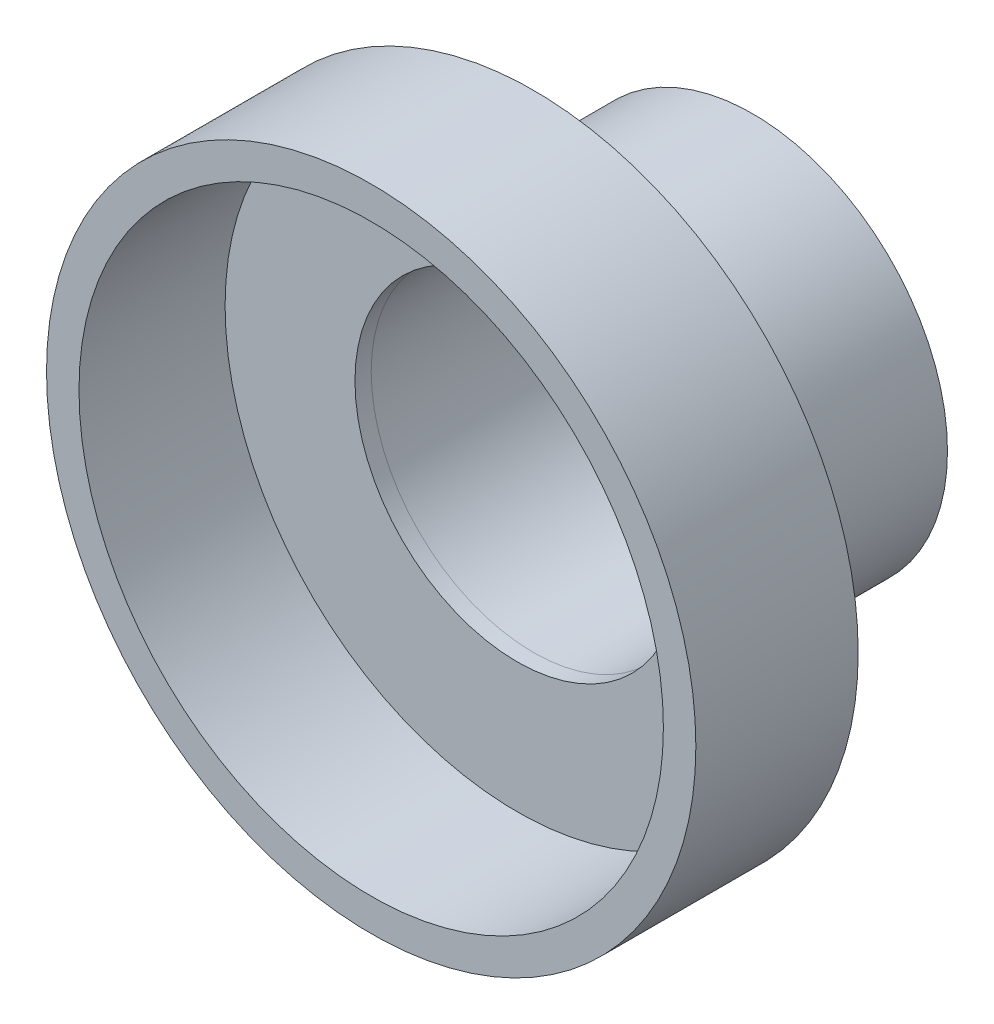
SolidWorks part; units mm, degrees
material "Delrin 2700 NC010, Low Viscosity Acetal Copolymer (SS)"
ref_plane "Front Plane" through (0, 0, 0) normal (0, 0, 1) x (1, 0, 0)
ref_plane "Top Plane" through (0, 0, 0) normal (0, 1, 0) x (1, 0, 0)
ref_plane "Right Plane" through (0, 0, 0) normal (1, 0, 0) x (0, 0, -1)
sketch "Sketch1" plane through (0, 0, 0) normal (0, 0, 1) x (1, 0, 0)
  circle A0 centre (0, 0) radius 2.5
  circle A1 centre (0, 0) radius 3
  dimension "D1" = 5
  dimension "D2" = 6
extrude "Boss-Extrude1" add sketch "Sketch1" along normal blind 3.375
sketch "Sketch2" plane through (0, 0, 3.375) normal (0, 0, 1) x (1, 0, 0)
  circle A0 centre (0, 0) radius 5
  circle A1 centre (0, 0) radius 4.5
  dimension "D1" = 9
extrude "Boss-Extrude2" add sketch "Sketch2" along normal blind 2.5
sketch "Sketch4" plane through (0, 0, 3.375) normal (0, 0, 1) x (1, 0, 0)
  circle A0 centre (0, 0) radius 4.5
  circle A1 centre (0, 0) radius 2.5
  circle A2 centre (0, 0) radius 2.5 construction
extrude "Boss-Extrude5" add sketch "Sketch4" along normal blind 0.25
